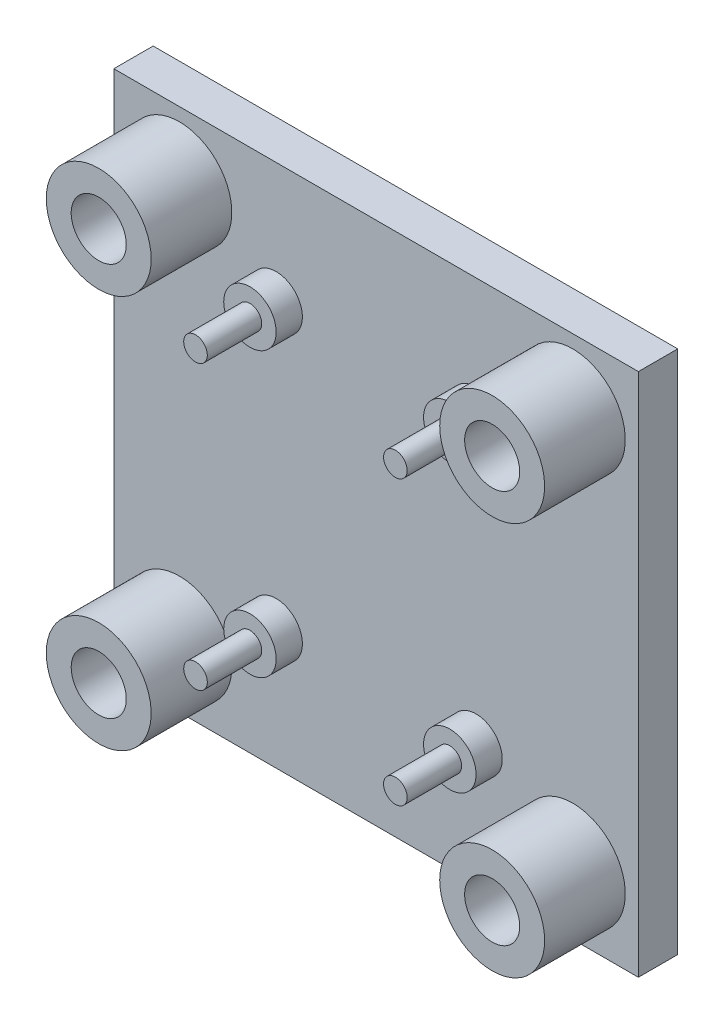
SolidWorks part; units mm, degrees
material "ABS"
ref_plane "前基準面" through (0, 0, 0) normal (0, 0, 1) x (1, 0, 0)
ref_plane "上基準面" through (0, 0, 0) normal (0, 1, 0) x (1, 0, 0)
ref_plane "右基準面" through (0, 0, 0) normal (1, 0, 0) x (0, 0, -1)
sketch "草圖1" plane through (0, 0, 0) normal (0, 0, 1) x (1, 0, 0)
  line L1 (-20, -20) -> (20, -20)
  line L2 (-20, -20) -> (-20, 20)
  line L3 (-20, 20) -> (20, 20)
  line L4 (20, -20) -> (20, 20)
  line L5 (-20, -20) -> (20, 20) construction
  line L6 (-20, 20) -> (20, -20) construction
  point P0 (0, 0)
  dimension "D1" = 40
  dimension "D2" = 40
extrude "填料-伸長1" add sketch "草圖1" along normal blind 3
sketch "草圖2" plane through (0, 0, 3) normal (0, 0, 1) x (1, 0, 0)
  line L0 (0, 20) -> (0, -20) construction
  line L1 (20, 20) -> (-20, 20) construction
  line L2 (-20, -20) -> (20, -20) construction
  line L3 (-20, 0) -> (20, 0) construction
  line L4 (-20, 20) -> (-20, -20) construction
  line L5 (20, -20) -> (20, 20) construction
  circle A0 centre (-7.62, 10.795) radius 2
  circle A1 centre (-7.62, -10.795) radius 2
  circle A2 centre (7.62, 10.795) radius 2
  circle A3 centre (7.62, -10.795) radius 2
  dimension "D1" = 4
  dimension "D2" = 7.62
  dimension "D3" = 10.795
extrude "填料-伸長2" add sketch "草圖2" along normal blind 2
sketch "草圖3" plane through (0, 0, 5) normal (0, 0, 1) x (1, 0, 0)
  line L0 (0, 20) -> (0, -20) construction
  line L1 (20, 0) -> (-20, 0) construction
  line L2 (20, -20) -> (20, 20) construction
  line L3 (-20, 20) -> (-20, -20) construction
  line L4 (20, 20) -> (-20, 20) construction
  line L5 (-20, -20) -> (20, -20) construction
  circle A0 centre (-7.62, 10.795) radius 0.9
  circle A1 centre (-7.62, -10.795) radius 0.9
  circle A2 centre (7.62, -10.795) radius 0.9
  circle A3 centre (7.62, 10.795) radius 0.9
  dimension "D1" = 1.8
extrude "填料-伸長3" add sketch "草圖3" along normal blind 4.15
sketch "草圖4" plane through (0, 0, 3) normal (0, 0, 1) x (1, 0, 0)
  line L0 (-20, 0) -> (20, 0) construction
  line L1 (-20, 20) -> (-20, -20) construction
  line L2 (20, -20) -> (20, 20) construction
  line L3 (0, 20) -> (0, -20) construction
  line L4 (20, 20) -> (-20, 20) construction
  line L5 (-20, -20) -> (20, -20) construction
  circle A0 centre (-15, 15) radius 4
  circle A1 centre (-15, -15) radius 4
  circle A2 centre (15, -15) radius 4
  circle A3 centre (15, 15) radius 4
  dimension "D1" = 15
  dimension "D2" = 15
  dimension "D3" = 8
extrude "填料-伸長4" add sketch "草圖4" along normal blind 6.15
sketch "草圖5" plane through (0, 0, 9.15) normal (0, 0, 1) x (1, 0, 0)
  line L0 (-20, 0) -> (20, 0) construction
  line L1 (0, 20) -> (0, -20) construction
  line L2 (-20, 20) -> (-20, -20) construction
  line L3 (20, 20) -> (-20, 20) construction
  line L4 (20, -20) -> (20, 20) construction
  line L5 (-20, -20) -> (20, -20) construction
  circle A0 centre (-15, 15) radius 2.1
  circle A1 centre (-15, -15) radius 2.1
  circle A2 centre (15, -15) radius 2.1
  circle A3 centre (15, 15) radius 2.1
  dimension "D1" = 4.2
extrude "除料-伸長1" cut sketch "草圖5" against normal through all
